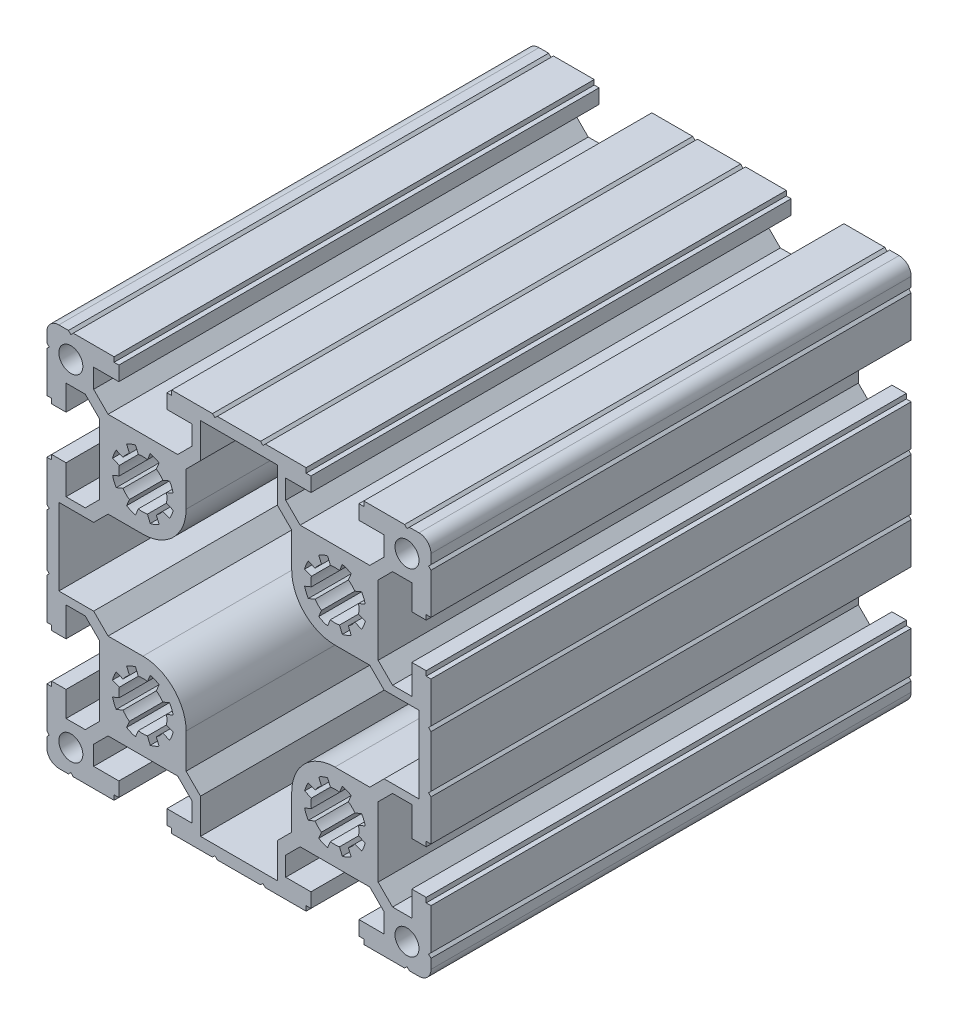
SolidWorks part; units mm, degrees
ref_plane "Ön Düzlem" through (0, 0, 0) normal (0, 0, 1) x (1, 0, 0)
ref_plane "Üst Düzlem" through (0, 0, 0) normal (0, 1, 0) x (1, 0, 0)
ref_plane "Sağ Düzlem" through (0, 0, 0) normal (1, 0, 0) x (0, 0, -1)
ref_plane "Düzlem1" through (0, 0, 100) normal (0, 0, 1) x (1, 0, 0)
sketch "Çizim1" plane through (0, 0, 100) normal (0, 0, 1) x (1, 0, 0)
  line L0 (15.0912, -19.0491) -> (13.6836, -18.466)
  line L1 (14.449, -16.6183) -> (15.8566, -17.2014)
  line L2 (17.2014, -15.8566) -> (16.6183, -14.449)
  line L3 (18.4661, -13.6836) -> (19.0491, -15.0912)
  line L4 (20.9509, -15.0912) -> (21.5339, -13.6836)
  line L5 (23.3817, -14.449) -> (22.7986, -15.8566)
  line L6 (24.1434, -17.2014) -> (25.551, -16.6183)
  line L7 (26.3164, -18.466) -> (24.9088, -19.0491)
  line L8 (24.9088, -20.9509) -> (26.3164, -21.5339)
  line L9 (25.551, -23.3817) -> (24.1434, -22.7986)
  line L10 (22.7986, -24.1434) -> (23.3817, -25.551)
  line L11 (21.5339, -26.3164) -> (20.9509, -24.9087)
  line L12 (19.0491, -24.9087) -> (18.4661, -26.3164)
  line L13 (16.6183, -25.551) -> (17.2014, -24.1434)
  line L14 (15.8566, -22.7986) -> (14.449, -23.3817)
  line L15 (13.6836, -21.5339) -> (15.0912, -20.9509)
  line L16 (-24.9088, -19.0491) -> (-26.3164, -18.466)
  line L17 (-25.551, -16.6183) -> (-24.1434, -17.2014)
  line L18 (-22.7986, -15.8566) -> (-23.3817, -14.449)
  line L19 (-21.5339, -13.6836) -> (-20.9509, -15.0912)
  line L20 (-19.0491, -15.0912) -> (-18.4661, -13.6836)
  line L21 (-16.6183, -14.449) -> (-17.2014, -15.8566)
  line L22 (-15.8566, -17.2014) -> (-14.449, -16.6183)
  line L23 (-13.6836, -18.466) -> (-15.0912, -19.0491)
  line L24 (-15.0912, -20.9509) -> (-13.6836, -21.5339)
  line L25 (-14.449, -23.3817) -> (-15.8566, -22.7986)
  line L26 (-17.2014, -24.1434) -> (-16.6183, -25.551)
  line L27 (-18.4661, -26.3164) -> (-19.0491, -24.9087)
  line L28 (-20.9509, -24.9087) -> (-21.5339, -26.3164)
  line L29 (-23.3817, -25.551) -> (-22.7986, -24.1434)
  line L30 (-24.1434, -22.7986) -> (-25.551, -23.3817)
  line L31 (-26.3164, -21.5339) -> (-24.9088, -20.9509)
  line L32 (-30.25, -8) -> (-37.5, -8)
  line L33 (-37.5, -8) -> (-37.5, 8)
  line L34 (-37.5, 8) -> (-30.25, 8)
  line L35 (-30.25, 8) -> (-27.25, 11)
  line L36 (-27.25, 11) -> (-20, 11)
  line L37 (-11, 20) -> (-11, 27.25)
  line L38 (-11, 27.25) -> (-8, 30.25)
  line L39 (-8, 30.25) -> (-8, 37.5)
  line L40 (-8, 37.5) -> (8, 37.5)
  line L41 (8, 37.5) -> (8, 30.25)
  line L42 (8, 30.25) -> (11, 27.25)
  line L43 (11, 27.25) -> (11, 20)
  line L44 (20, 11) -> (27.25, 11)
  line L45 (27.25, 11) -> (30.25, 8)
  line L46 (30.25, 8) -> (37.5, 8)
  line L47 (37.5, 8) -> (37.5, -8)
  line L48 (37.5, -8) -> (30.25, -8)
  line L49 (30.25, -8) -> (27.25, -11)
  line L50 (27.25, -11) -> (20, -11)
  line L51 (11, -20) -> (11, -27.25)
  line L52 (11, -27.25) -> (8, -30.25)
  line L53 (8, -30.25) -> (8, -37.5)
  line L54 (8, -37.5) -> (-8, -37.5)
  line L55 (-8, -37.5) -> (-8, -30.25)
  line L56 (-8, -30.25) -> (-11, -27.25)
  line L57 (-11, -27.25) -> (-11, -20)
  line L58 (-20, -11) -> (-27.25, -11)
  line L59 (-27.25, -11) -> (-30.25, -8)
  line L60 (32, 9.75) -> (29, 12.75)
  line L61 (29, 12.75) -> (29, 27.25)
  line L62 (29, 27.25) -> (32, 30.25)
  line L63 (32, 30.25) -> (36, 30.25)
  line L64 (36, 30.25) -> (36, 25)
  line L65 (36, 25) -> (39, 25)
  line L66 (39, 25) -> (39, 26)
  line L67 (39, 26) -> (40, 26)
  line L68 (40, 26) -> (40, 34.5)
  line L69 (40, 34.5) -> (39.5, 35)
  line L70 (39.5, 35) -> (40, 35.5)
  line L71 (40, 35.5) -> (40, 37.5)
  line L72 (37.5, 40) -> (35.5, 40)
  line L73 (35.5, 40) -> (35, 39.5)
  line L74 (35, 39.5) -> (34.5, 40)
  line L75 (34.5, 40) -> (26, 40)
  line L76 (26, 40) -> (26, 39)
  line L77 (26, 39) -> (25, 39)
  line L78 (25, 39) -> (25, 36)
  line L79 (25, 36) -> (30.25, 36)
  line L80 (30.25, 36) -> (30.25, 32)
  line L81 (30.25, 32) -> (27.25, 29)
  line L82 (27.25, 29) -> (12.75, 29)
  line L83 (12.75, 29) -> (9.75, 32)
  line L84 (9.75, 32) -> (9.75, 36)
  line L85 (9.75, 36) -> (15, 36)
  line L86 (15, 36) -> (15, 39)
  line L87 (15, 39) -> (14, 39)
  line L88 (14, 39) -> (14, 40)
  line L89 (14, 40) -> (5.5, 40)
  line L90 (5.5, 40) -> (5, 39.5)
  line L91 (5, 39.5) -> (4.5, 40)
  line L92 (4.5, 40) -> (-4.5, 40)
  line L93 (-4.5, 40) -> (-5, 39.5)
  line L94 (-5, 39.5) -> (-5.5, 40)
  line L95 (-5.5, 40) -> (-14, 40)
  line L96 (-14, 40) -> (-14, 39)
  line L97 (-14, 39) -> (-15, 39)
  line L98 (-15, 39) -> (-15, 36)
  line L99 (-15, 36) -> (-9.75, 36)
  line L100 (-9.75, 36) -> (-9.75, 32)
  line L101 (-9.75, 32) -> (-12.75, 29)
  line L102 (-12.75, 29) -> (-27.25, 29)
  line L103 (-27.25, 29) -> (-30.25, 32)
  line L104 (-30.25, 32) -> (-30.25, 36)
  line L105 (-30.25, 36) -> (-25, 36)
  line L106 (-25, 36) -> (-25, 39)
  line L107 (-25, 39) -> (-26, 39)
  line L108 (-26, 39) -> (-26, 40)
  line L109 (-26, 40) -> (-34.5, 40)
  line L110 (-34.5, 40) -> (-35, 39.5)
  line L111 (-35, 39.5) -> (-35.5, 40)
  line L112 (-35.5, 40) -> (-37.5, 40)
  line L113 (-40, 37.5) -> (-40, 35.5)
  line L114 (-40, 35.5) -> (-39.5, 35)
  line L115 (-39.5, 35) -> (-40, 34.5)
  line L116 (-40, 34.5) -> (-40, 26)
  line L117 (-40, 26) -> (-39, 26)
  line L118 (-39, 26) -> (-39, 25)
  line L119 (-39, 25) -> (-36, 25)
  line L120 (-36, 25) -> (-36, 30.25)
  line L121 (-36, 30.25) -> (-32, 30.25)
  line L122 (-32, 30.25) -> (-29, 27.25)
  line L123 (-29, 27.25) -> (-29, 12.75)
  line L124 (-29, 12.75) -> (-32, 9.75)
  line L125 (-32, 9.75) -> (-36, 9.75)
  line L126 (-36, 9.75) -> (-36, 15.8849)
  line L127 (-36, 15.8849) -> (-39, 15.8849)
  line L128 (-39, 15.8849) -> (-39, 14.8849)
  line L129 (-39, 14.8849) -> (-40, 14.8849)
  line L130 (-40, 14.8849) -> (-40, 6.3849)
  line L131 (-40, 6.3849) -> (-39.5, 5.8849)
  line L132 (-39.5, 5.8849) -> (-40, 5.3849)
  line L133 (-40, 5.3849) -> (-40, -5.3849)
  line L134 (-40, -5.3849) -> (-39.5, -5.8849)
  line L135 (-39.5, -5.8849) -> (-40, -6.3849)
  line L136 (-40, -6.3849) -> (-40, -14.8849)
  line L137 (-40, -14.8849) -> (-39, -14.8849)
  line L138 (-39, -14.8849) -> (-39, -15.8849)
  line L139 (-39, -15.8849) -> (-36, -15.8849)
  line L140 (-36, -15.8849) -> (-36, -9.75)
  line L141 (-36, -9.75) -> (-32, -9.75)
  line L142 (-32, -9.75) -> (-29, -12.75)
  line L143 (-29, -12.75) -> (-29, -27.25)
  line L144 (-29, -27.25) -> (-32, -30.25)
  line L145 (-32, -30.25) -> (-36, -30.25)
  line L146 (-36, -30.25) -> (-36, -25)
  line L147 (-36, -25) -> (-39, -25)
  line L148 (-39, -25) -> (-39, -26)
  line L149 (-39, -26) -> (-40, -26)
  line L150 (-40, -26) -> (-40, -34.5)
  line L151 (-40, -34.5) -> (-39.5, -35)
  line L152 (-39.5, -35) -> (-40, -35.5)
  line L153 (-40, -35.5) -> (-40, -37.5)
  line L154 (-37.5, -40) -> (-35.5, -40)
  line L155 (-35.5, -40) -> (-35, -39.5)
  line L156 (-35, -39.5) -> (-34.5, -40)
  line L157 (-34.5, -40) -> (-26, -40)
  line L158 (-26, -40) -> (-26, -39)
  line L159 (-26, -39) -> (-25, -39)
  line L160 (-25, -39) -> (-25, -36)
  line L161 (-25, -36) -> (-30.25, -36)
  line L162 (-30.25, -36) -> (-30.25, -32)
  line L163 (-30.25, -32) -> (-27.25, -29)
  line L164 (-27.25, -29) -> (-12.75, -29)
  line L165 (-12.75, -29) -> (-9.75, -32)
  line L166 (-9.75, -32) -> (-9.75, -36)
  line L167 (-9.75, -36) -> (-15, -36)
  line L168 (-15, -36) -> (-15, -39)
  line L169 (-15, -39) -> (-14, -39)
  line L170 (-14, -39) -> (-14, -40)
  line L171 (-14, -40) -> (-5.5, -40)
  line L172 (-5.5, -40) -> (-5, -39.5)
  line L173 (-5, -39.5) -> (-4.5, -40)
  line L174 (-4.5, -40) -> (4.5, -40)
  line L175 (4.5, -40) -> (5, -39.5)
  line L176 (5, -39.5) -> (5.5, -40)
  line L177 (5.5, -40) -> (14, -40)
  line L178 (14, -40) -> (14, -39)
  line L179 (14, -39) -> (15, -39)
  line L180 (15, -39) -> (15, -36)
  line L181 (15, -36) -> (9.75, -36)
  line L182 (9.75, -36) -> (9.75, -32)
  line L183 (9.75, -32) -> (12.75, -29)
  line L184 (12.75, -29) -> (27.25, -29)
  line L185 (27.25, -29) -> (30.25, -32)
  line L186 (30.25, -32) -> (30.25, -36)
  line L187 (30.25, -36) -> (25, -36)
  line L188 (25, -36) -> (25, -39)
  line L189 (25, -39) -> (26, -39)
  line L190 (26, -39) -> (26, -40)
  line L191 (26, -40) -> (34.5, -40)
  line L192 (34.5, -40) -> (35, -39.5)
  line L193 (35, -39.5) -> (35.5, -40)
  line L194 (35.5, -40) -> (37.5, -40)
  line L195 (40, -37.5) -> (40, -35.5)
  line L196 (40, -35.5) -> (39.5, -35)
  line L197 (39.5, -35) -> (40, -34.5)
  line L198 (40, -34.5) -> (40, -26)
  line L199 (40, -26) -> (39, -26)
  line L200 (39, -26) -> (39, -25)
  line L201 (39, -25) -> (36, -25)
  line L202 (36, -25) -> (36, -30.25)
  line L203 (36, -30.25) -> (32, -30.25)
  line L204 (32, -30.25) -> (29, -27.25)
  line L205 (29, -27.25) -> (29, -12.75)
  line L206 (29, -12.75) -> (32, -9.75)
  line L207 (32, -9.75) -> (36, -9.75)
  line L208 (36, -9.75) -> (36, -15.8849)
  line L209 (36, -15.8849) -> (39, -15.8849)
  line L210 (39, -15.8849) -> (39, -14.8849)
  line L211 (39, -14.8849) -> (40, -14.8849)
  line L212 (40, -14.8849) -> (40, -6.3849)
  line L213 (40, -6.3849) -> (39.5, -5.8849)
  line L214 (39.5, -5.8849) -> (40, -5.3849)
  line L215 (40, -5.3849) -> (40, 5.3849)
  line L216 (40, 5.3849) -> (39.5, 5.8849)
  line L217 (39.5, 5.8849) -> (40, 6.3849)
  line L218 (40, 6.3849) -> (40, 14.8849)
  line L219 (40, 14.8849) -> (39, 14.8849)
  line L220 (39, 14.8849) -> (39, 15.8849)
  line L221 (39, 15.8849) -> (36, 15.8849)
  line L222 (36, 15.8849) -> (36, 9.75)
  line L223 (36, 9.75) -> (32, 9.75)
  line L224 (-24.9088, 20.9509) -> (-26.3164, 21.5339)
  line L225 (-25.551, 23.3817) -> (-24.1434, 22.7986)
  line L226 (-22.7986, 24.1434) -> (-23.3817, 25.551)
  line L227 (-21.5339, 26.3164) -> (-20.9509, 24.9087)
  line L228 (-19.0491, 24.9087) -> (-18.4661, 26.3164)
  line L229 (-16.6183, 25.551) -> (-17.2014, 24.1434)
  line L230 (-15.8566, 22.7986) -> (-14.449, 23.3817)
  line L231 (-13.6836, 21.5339) -> (-15.0912, 20.9509)
  line L232 (-15.0912, 19.0491) -> (-13.6836, 18.466)
  line L233 (-14.449, 16.6183) -> (-15.8566, 17.2014)
  line L234 (-17.2014, 15.8566) -> (-16.6183, 14.449)
  line L235 (-18.4661, 13.6836) -> (-19.0491, 15.0912)
  line L236 (-20.9509, 15.0912) -> (-21.5339, 13.6836)
  line L237 (-23.3817, 14.449) -> (-22.7986, 15.8566)
  line L238 (-24.1434, 17.2014) -> (-25.551, 16.6183)
  line L239 (-26.3164, 18.466) -> (-24.9088, 19.0491)
  line L240 (15.0912, 20.9509) -> (13.6836, 21.5339)
  line L241 (14.449, 23.3817) -> (15.8566, 22.7986)
  line L242 (17.2014, 24.1434) -> (16.6183, 25.551)
  line L243 (18.4661, 26.3164) -> (19.0491, 24.9087)
  line L244 (20.9509, 24.9087) -> (21.5339, 26.3164)
  line L245 (23.3817, 25.551) -> (22.7986, 24.1434)
  line L246 (24.1434, 22.7986) -> (25.551, 23.3817)
  line L247 (26.3164, 21.5339) -> (24.9088, 20.9509)
  line L248 (24.9088, 19.0491) -> (26.3164, 18.466)
  line L249 (25.551, 16.6183) -> (24.1434, 17.2014)
  line L250 (22.7986, 15.8566) -> (23.3817, 14.449)
  line L251 (21.5339, 13.6836) -> (20.9509, 15.0912)
  line L252 (19.0491, 15.0912) -> (18.4661, 13.6836)
  line L253 (16.6183, 14.449) -> (17.2014, 15.8566)
  line L254 (15.8566, 17.2014) -> (14.449, 16.6183)
  line L255 (13.6836, 18.466) -> (15.0912, 19.0491)
  arc A0 (13.6836, -18.466) -> (14.449, -16.6183) centre (20, -20) cw
  arc A1 (15.8566, -17.2014) -> (17.2014, -15.8566) centre (20, -20) cw
  arc A2 (16.6183, -14.449) -> (18.4661, -13.6836) centre (20, -20) cw
  arc A3 (19.0491, -15.0912) -> (20.9509, -15.0912) centre (20, -20) cw
  arc A4 (21.5339, -13.6836) -> (23.3817, -14.449) centre (20, -20) cw
  arc A5 (22.7986, -15.8566) -> (24.1434, -17.2014) centre (20, -20) cw
  arc A6 (25.551, -16.6183) -> (26.3164, -18.466) centre (20, -20) cw
  arc A7 (24.9088, -19.0491) -> (24.9088, -20.9509) centre (20, -20) cw
  arc A8 (26.3164, -21.5339) -> (25.551, -23.3817) centre (20, -20) cw
  arc A9 (24.1434, -22.7986) -> (22.7986, -24.1434) centre (20, -20) cw
  arc A10 (23.3817, -25.551) -> (21.5339, -26.3164) centre (20, -20) cw
  arc A11 (20.9509, -24.9087) -> (19.0491, -24.9087) centre (20, -20) cw
  arc A12 (18.4661, -26.3164) -> (16.6183, -25.551) centre (20, -20) cw
  arc A13 (17.2014, -24.1434) -> (15.8566, -22.7986) centre (20, -20) cw
  arc A14 (14.449, -23.3817) -> (13.6836, -21.5339) centre (20, -20) cw
  arc A15 (15.0912, -20.9509) -> (15.0912, -19.0491) centre (20, -20) cw
  arc A16 (-26.3164, -18.466) -> (-25.551, -16.6183) centre (-20, -20) cw
  arc A17 (-24.1434, -17.2014) -> (-22.7986, -15.8566) centre (-20, -20) cw
  arc A18 (-23.3817, -14.449) -> (-21.5339, -13.6836) centre (-20, -20) cw
  arc A19 (-20.9509, -15.0912) -> (-19.0491, -15.0912) centre (-20, -20) cw
  arc A20 (-18.4661, -13.6836) -> (-16.6183, -14.449) centre (-20, -20) cw
  arc A21 (-17.2014, -15.8566) -> (-15.8566, -17.2014) centre (-20, -20) cw
  arc A22 (-14.449, -16.6183) -> (-13.6836, -18.466) centre (-20, -20) cw
  arc A23 (-15.0912, -19.0491) -> (-15.0912, -20.9509) centre (-20, -20) cw
  arc A24 (-13.6836, -21.5339) -> (-14.449, -23.3817) centre (-20, -20) cw
  arc A25 (-15.8566, -22.7986) -> (-17.2014, -24.1434) centre (-20, -20) cw
  arc A26 (-16.6183, -25.551) -> (-18.4661, -26.3164) centre (-20, -20) cw
  arc A27 (-19.0491, -24.9087) -> (-20.9509, -24.9087) centre (-20, -20) cw
  arc A28 (-21.5339, -26.3164) -> (-23.3817, -25.551) centre (-20, -20) cw
  arc A29 (-22.7986, -24.1434) -> (-24.1434, -22.7986) centre (-20, -20) cw
  arc A30 (-25.551, -23.3817) -> (-26.3164, -21.5339) centre (-20, -20) cw
  arc A31 (-24.9088, -20.9509) -> (-24.9088, -19.0491) centre (-20, -20) cw
  circle A32 centre (35, 35) radius 2.5
  circle A33 centre (35, -35) radius 2.5
  circle A34 centre (-35, 35) radius 2.5
  circle A35 centre (-35, -35) radius 2.5
  arc A36 (-20, 11) -> (-11, 20) centre (-20, 20) ccw
  arc A37 (11, 20) -> (20, 11) centre (20, 20) ccw
  arc A38 (20, -11) -> (11, -20) centre (20, -20) ccw
  arc A39 (-11, -20) -> (-20, -11) centre (-20, -20) ccw
  arc A40 (40, 37.5) -> (37.5, 40) centre (37.5, 37.5) ccw
  arc A41 (-37.5, 40) -> (-40, 37.5) centre (-37.5, 37.5) ccw
  arc A42 (-40, -37.5) -> (-37.5, -40) centre (-37.5, -37.5) ccw
  arc A43 (37.5, -40) -> (40, -37.5) centre (37.5, -37.5) ccw
  arc A44 (-26.3164, 21.5339) -> (-25.551, 23.3817) centre (-20, 20) cw
  arc A45 (-24.1434, 22.7986) -> (-22.7986, 24.1434) centre (-20, 20) cw
  arc A46 (-23.3817, 25.551) -> (-21.5339, 26.3164) centre (-20, 20) cw
  arc A47 (-20.9509, 24.9087) -> (-19.0491, 24.9087) centre (-20, 20) cw
  arc A48 (-18.4661, 26.3164) -> (-16.6183, 25.551) centre (-20, 20) cw
  arc A49 (-17.2014, 24.1434) -> (-15.8566, 22.7986) centre (-20, 20) cw
  arc A50 (-14.449, 23.3817) -> (-13.6836, 21.5339) centre (-20, 20) cw
  arc A51 (-15.0912, 20.9509) -> (-15.0912, 19.0491) centre (-20, 20) cw
  arc A52 (-13.6836, 18.466) -> (-14.449, 16.6183) centre (-20, 20) cw
  arc A53 (-15.8566, 17.2014) -> (-17.2014, 15.8566) centre (-20, 20) cw
  arc A54 (-16.6183, 14.449) -> (-18.4661, 13.6836) centre (-20, 20) cw
  arc A55 (-19.0491, 15.0912) -> (-20.9509, 15.0912) centre (-20, 20) cw
  arc A56 (-21.5339, 13.6836) -> (-23.3817, 14.449) centre (-20, 20) cw
  arc A57 (-22.7986, 15.8566) -> (-24.1434, 17.2014) centre (-20, 20) cw
  arc A58 (-25.551, 16.6183) -> (-26.3164, 18.466) centre (-20, 20) cw
  arc A59 (-24.9088, 19.0491) -> (-24.9088, 20.9509) centre (-20, 20) cw
  arc A60 (13.6836, 21.5339) -> (14.449, 23.3817) centre (20, 20) cw
  arc A61 (15.8566, 22.7986) -> (17.2014, 24.1434) centre (20, 20) cw
  arc A62 (16.6183, 25.551) -> (18.4661, 26.3164) centre (20, 20) cw
  arc A63 (19.0491, 24.9087) -> (20.9509, 24.9087) centre (20, 20) cw
  arc A64 (21.5339, 26.3164) -> (23.3817, 25.551) centre (20, 20) cw
  arc A65 (22.7986, 24.1434) -> (24.1434, 22.7986) centre (20, 20) cw
  arc A66 (25.551, 23.3817) -> (26.3164, 21.5339) centre (20, 20) cw
  arc A67 (24.9088, 20.9509) -> (24.9088, 19.0491) centre (20, 20) cw
  arc A68 (26.3164, 18.466) -> (25.551, 16.6183) centre (20, 20) cw
  arc A69 (24.1434, 17.2014) -> (22.7986, 15.8566) centre (20, 20) cw
  arc A70 (23.3817, 14.449) -> (21.5339, 13.6836) centre (20, 20) cw
  arc A71 (20.9509, 15.0912) -> (19.0491, 15.0912) centre (20, 20) cw
  arc A72 (18.4661, 13.6836) -> (16.6183, 14.449) centre (20, 20) cw
  arc A73 (17.2014, 15.8566) -> (15.8566, 17.2014) centre (20, 20) cw
  arc A74 (14.449, 16.6183) -> (13.6836, 18.466) centre (20, 20) cw
  arc A75 (15.0912, 19.0491) -> (15.0912, 20.9509) centre (20, 20) cw
extrude "Yükseklik-Ekstrüzyon1" add sketch "Çizim1" against normal blind 100
